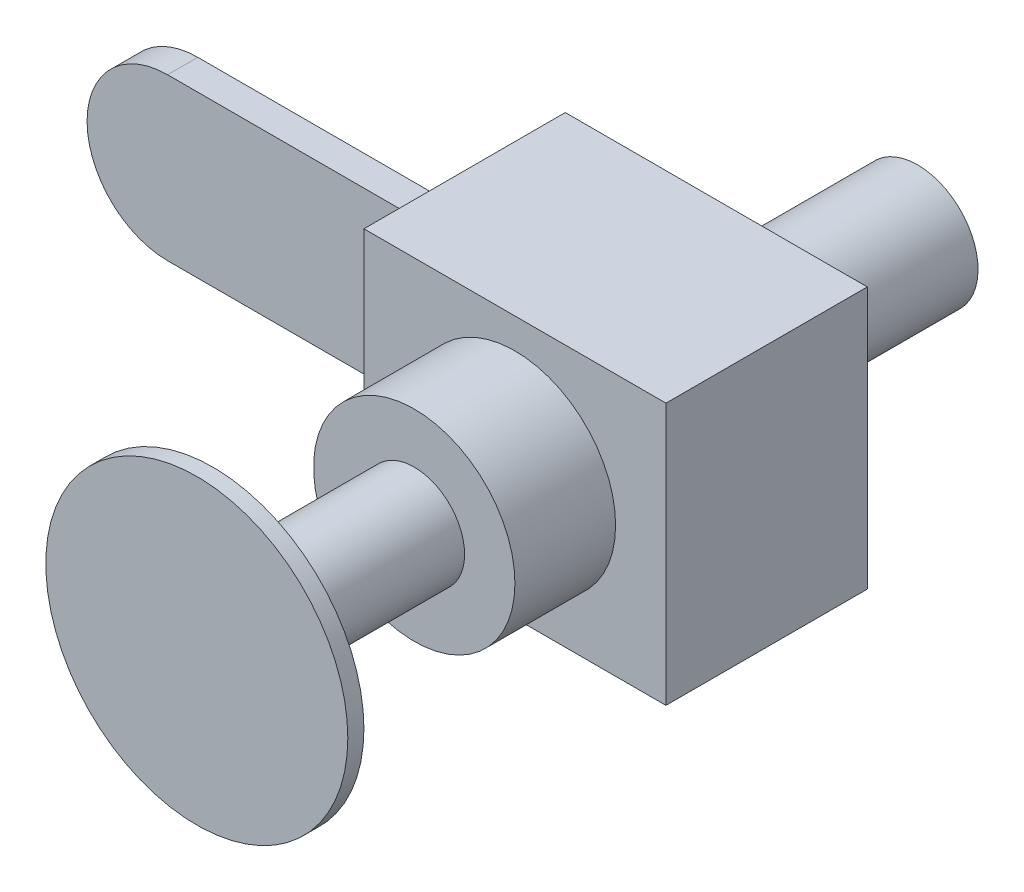
SolidWorks part; units mm, degrees
ref_plane "Front Plane" through (0, 0, 0) normal (0, 0, 1) x (1, 0, 0)
ref_plane "Top Plane" through (0, 0, 0) normal (0, 1, 0) x (1, 0, 0)
ref_plane "Right Plane" through (0, 0, 0) normal (1, 0, 0) x (0, 0, -1)
sketch "Sketch1" plane through (0, 0, 0) normal (0, 0, 1) x (1, 0, 0)
  line L0 (0, 40) -> (140, 40)
  line L1 (140, 40) -> (140, -40)
  line L2 (140, -40) -> (0, -40)
  arc A0 (0, 40) -> (0, -40) centre (0, 0) ccw
  dimension "D1" = 80
  dimension "180" = 140
extrude "Boss-Extrude1" add sketch "Sketch1" along normal mid plane 15
sketch "Sketch3" plane through (140, 0, 0) normal (1, 0, 0) x (0, 0, -1)
  line L1 (-50, 65) -> (50, 65)
  line L2 (-50, 65) -> (-50, -65)
  line L3 (-50, -65) -> (50, -65)
  line L4 (50, 65) -> (50, -65)
  line L5 (-50, 65) -> (50, -65) construction
  line L6 (-50, -65) -> (50, 65) construction
  point P0 (0, 0)
  dimension "D1" = 100
  dimension "D2" = 130
extrude "Boss-Extrude2" add sketch "Sketch3" along normal blind 150
sketch "Sketch4" plane through (0, 0, -50) normal (0, 0, -1) x (-1, 0, 0)
  line L0 (-290, 65) -> (-140, 65) construction
  circle A0 centre (-215, 0) radius 30
  point P2 (0, 0)
  point P5 (-215, 65)
  point P6 (0, 0)
  dimension "D1" = 60
extrude "Boss-Extrude3" add sketch "Sketch4" along normal blind 100
sketch "Sketch5" plane through (0, 0, 50) normal (0, 0, 1) x (1, 0, 0)
  line L0 (290, -65) -> (140, -65) construction
  circle A0 centre (215, 0) radius 50
  point P2 (0, 0)
  point P5 (215, -65)
  point P6 (0, 0)
  dimension "D1" = 100
extrude "Boss-Extrude4" add sketch "Sketch5" along normal blind 50
sketch "Sketch6" plane through (0, 0, 100) normal (0, 0, 1) x (1, 0, 0)
  circle A0 centre (215, 0) radius 25
extrude "Boss-Extrude5" add sketch "Sketch6" along normal blind 100
sketch "Sketch7" plane through (0, 0, 200) normal (0, 0, 1) x (1, 0, 0)
  circle A0 centre (215, 0) radius 75
extrude "Boss-Extrude6" add sketch "Sketch7" along normal blind 8
sketch "Sketch8" plane through (0, 0, -7.5) normal (0, 0, -1) x (-1, 0, 0)
  point P0 (0, 0)
